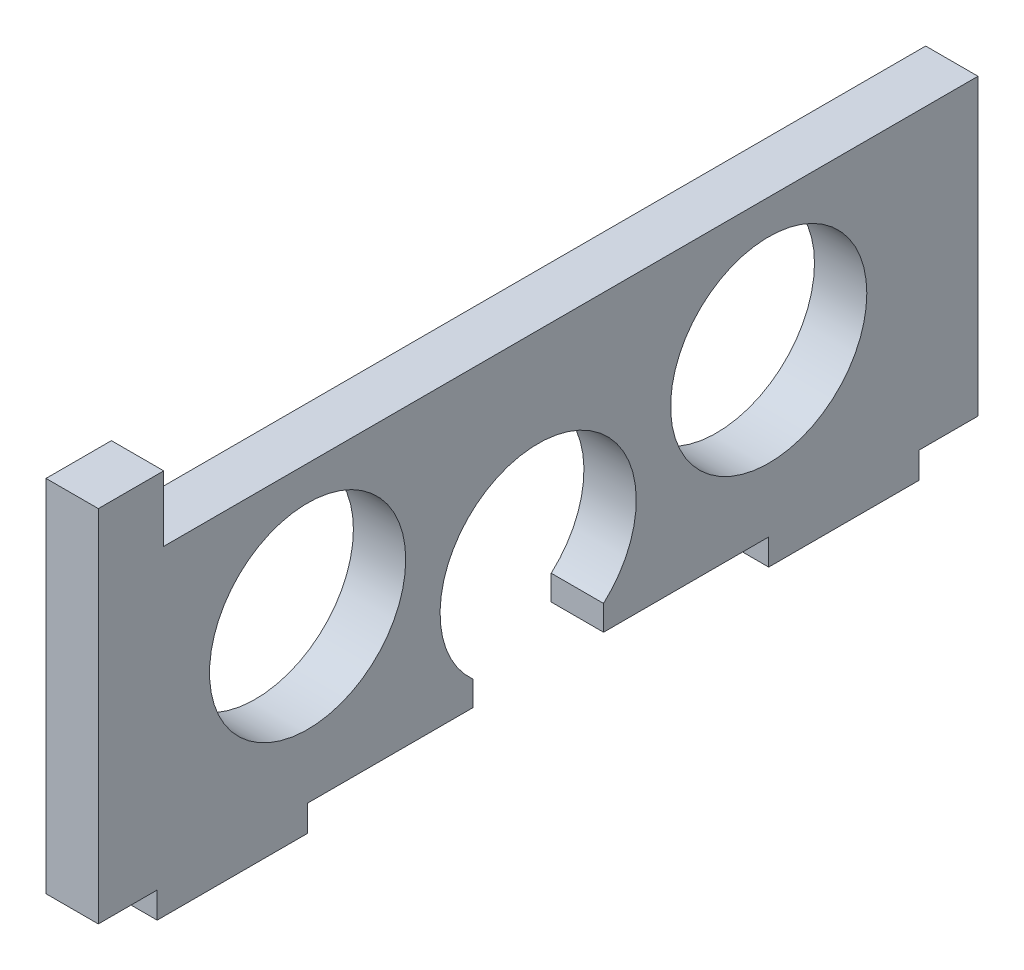
SolidWorks part; units mm, degrees
ref_plane "정면" through (0, 0, 0) normal (0, 0, 1) x (1, 0, 0)
ref_plane "윗면" through (0, 0, 0) normal (0, 1, 0) x (1, 0, 0)
ref_plane "우측면" through (0, 0, 0) normal (1, 0, 0) x (0, 0, -1)
sketch "스케치1" plane through (0, 0, 0) normal (1, 0, 0) x (0, 0, -1)
  line L0 (-9.5123, 0) -> (14.4726, 0) construction
  line L1 (-7.05, 1.3) -> (-7.05, 0.5)
  line L2 (-24.2092, 1.3) -> (25.0232, 1.3)
  line L3 (-24.2092, 1.3) -> (-24.2092, 0.5)
  line L4 (-24.2092, 0.5) -> (25.0232, 0.5)
  line L5 (25.0232, 1.3) -> (25.0232, 0.5)
  line L10 (7.05, 1.3) -> (7.05, 0.5)
  line L11 (11.65, 1.3) -> (11.65, 0.5)
  line L12 (-11.65, 1.3) -> (-11.65, 0.5)
  circle A0 centre (-7.05, 6.25) radius 6.25
  circle A1 centre (7.05, 6.25) radius 6.25
  circle A2 centre (0, 4.3) radius 1.8
  circle A3 centre (0, 4.3) radius 3
  circle A4 centre (-7.05, 6.25) radius 5.4
  circle A5 centre (7.05, 6.25) radius 5.4
  circle A6 centre (19.8088, 3.7) radius 2.4
  circle A7 centre (19.8088, 3.7) radius 2.95
  circle A8 centre (-7.05, 6.25) radius 3
  circle A9 centre (7.05, 6.25) radius 3
  point P23 (21.5242, 1.3)
  point P24 (18.0934, 1.3)
  dimension "D1" = 12.5
  dimension "D2" = 3.6
  dimension "D3" = 6
  dimension "D4" = 10.8
  dimension "D11" = 5.9
  dimension "D12" = 4.8
  dimension "D14" = 6
  dimension "D15" = 6
  dimension "D5" = 14.1
  dimension "D6" = 7.05
  dimension "D7" = 0.8
  dimension "D8" = 4.6
  dimension "D9" = 4.6
  dimension "D13" = 1
sketch "스케치2" plane through (0, 0, 0) normal (1, 0, 0) x (0, 0, -1)
  line L0 (-13.45, 1.3) -> (-11.65, 1.3)
  line L1 (-24.2092, 1.3) -> (25.0232, 1.3) construction
  line L2 (-11.65, 1.3) -> (-11.65, 0.5)
  line L3 (-11.65, 0.5) -> (-7.05, 0.5)
  line L4 (-7.05, 0.5) -> (-7.05, 1.3)
  line L5 (-7.05, 1.3) -> (-2, 1.3)
  line L6 (0, 55) -> (0, -55) construction
  line L7 (-13.45, 1.3) -> (-13.45, 12.3)
  line L8 (-13.45, 12.3) -> (-11.45, 12.3)
  line L9 (-11.45, 12.3) -> (-11.45, 10.3)
  line L10 (-2, 1.3) -> (-2, 2.0639)
  line L11 (-11.45, 10.3) -> (13.45, 10.3)
  line L12 (13.45, 10.3) -> (13.45, 1.3)
  line L13 (13.45, 1.3) -> (11.65, 1.3)
  line L14 (11.65, 1.3) -> (11.65, 0.5)
  line L15 (11.65, 0.5) -> (7.05, 0.5)
  line L16 (7.05, 0.5) -> (7.05, 1.3)
  line L17 (7.05, 1.3) -> (2, 1.3)
  line L18 (2, 1.3) -> (2, 2.0639)
  circle A0 centre (-7.05, 6.25) radius 3 construction
  circle A1 centre (-7.05, 6.25) radius 3
  circle A2 centre (7.05, 6.25) radius 3 construction
  circle A3 centre (7.05, 6.25) radius 3
  arc A8 (-2, 2.0639) -> (2, 2.0639) centre (0, 4.3) cw
  circle A9 centre (0, 4.3) radius 3 construction
  dimension "D1" = 1.8
  dimension "D2" = 2
  dimension "D3" = 2
  dimension "D4" = 6
  dimension "D7" = 2
sketch "스케치3" plane through (0, 0, 0) normal (1, 0, 0) x (0, 0, -1)
  line L0 (-2.5, 0) -> (2.5, 0)
  line L1 (-200009.5123, 0) -> (200014.4726, 0) construction
  line L3 (-2.5, 0) -> (-2.5, 0.8)
  line L4 (-2.5, 0.8) -> (-2.7, 0.8)
  line L5 (-2.7, 0.8) -> (-2.7, 9.25)
  line L6 (-2.7, 9.25) -> (2.7, 9.25)
  line L8 (0, 55) -> (0, -55) construction
  line L10 (2.5, 0.8) -> (2.7, 0.8)
  line L11 (2.5, 0) -> (2.5, 0.8)
  line L12 (2.7, 0.8) -> (2.7, 9.25)
  dimension "D3" = 8.45
  dimension "D4" = 0.8
extrude "보스-돌출1" add sketch "스케치2" along normal blind 1.6 contours L11 L12 L13 L14 L15 L16 L17 L18 A8 L10 L5 L4 L3 L2 L0 L7 L8 L9 | A1 | A3
